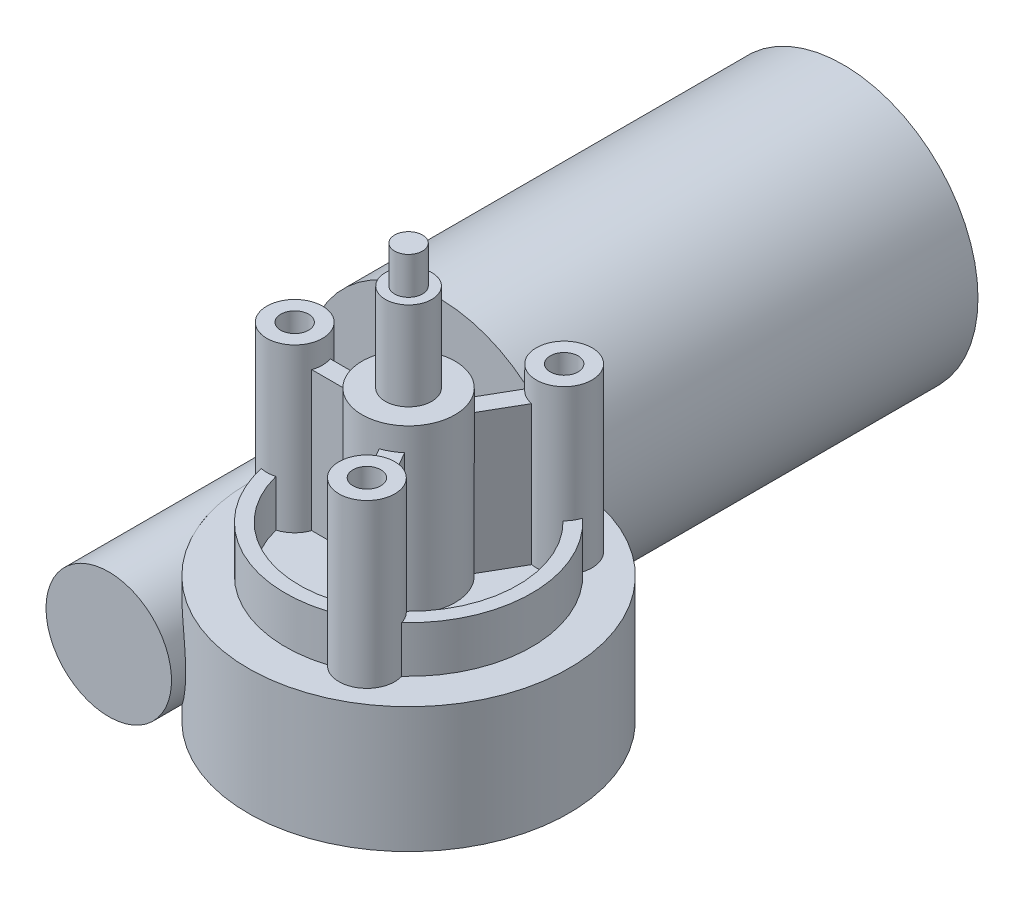
SolidWorks part; units mm, degrees
ref_plane "Front Plane" through (0, 0, 0) normal (0, 0, 1) x (1, 0, 0)
ref_plane "Top Plane" through (0, 0, 0) normal (0, 1, 0) x (1, 0, 0)
ref_plane "Right Plane" through (0, 0, 0) normal (1, 0, 0) x (0, 0, -1)
sketch "Sketch1" plane through (0, 0, 0) normal (0, 0, 1) x (1, 0, 0)
  circle A0 centre (0, 0) radius 29
  dimension "D1" = 58
extrude "Boss-Extrude1" add sketch "Sketch1" along normal blind 87
sketch "Sketch3" plane through (0, 0, 0) normal (0, 1, 0) x (1, 0, 0)
  line L0 (0, 0) -> (0, -87) construction
  line L1 (-29, -87) -> (29, -87) construction
  line L3 (0, 10) -> (-13.5, 10)
  line L4 (0, 10) -> (0, -158)
  line L5 (0, -158) -> (-13.5, -158)
  line L6 (-13.5, 10) -> (-13.5, -158)
  dimension "D3" = 13.5
  dimension "D1" = 168
  dimension "D2" = 10
revolve "Revolve1" add sketch "Sketch3" angle 360 about L0
sketch "Sketch4" plane through (0, 0, 0) normal (0, 1, 0) x (1, 0, 0)
  line L0 (0, -87) -> (0, 0) construction
  line L1 (-13.5, -87) -> (13.5, -87) construction
  line L2 (33, -161) -> (75.2332, -161) construction
  line L3 (13.5, 10) -> (-13.5, 10) construction
  circle A0 centre (33, -126.5) radius 34.5
  dimension "D1" = 69
  dimension "D2" = 33
  dimension "D3" = 171
extrude "Boss-Extrude2" add sketch "Sketch4" along normal mid plane 27
sketch "Sketch5" plane through (0, 13.5, 0) normal (0, 1, 0) x (1, 0, 0)
  line L0 (-1.5, -126.5) -> (67.5, -126.5) construction
  line L1 (33, -92) -> (33, -161) construction
  arc A0 (0, -116.4377) -> (0, -136.5623) centre (33, -126.5) ccw construction
  arc A1 (0, -136.5623) -> (0, -116.4377) centre (33, -126.5) ccw construction
  circle A2 centre (33, -126.5) radius 24.5 construction
  circle A3 centre (8.5, -126.5) radius 6
  circle A4 centre (33, -126.5) radius 10
  circle A5 centre (45.25, -105.2824) radius 6
  circle A6 centre (45.25, -147.7176) radius 6
  point P22 (33, -126.5)
  dimension "D1" = 49
  dimension "D2" = 20
  dimension "D3" = 12
  dimension "D4" = 3
extrude "Boss-Extrude3" add sketch "Sketch5" along normal blind 35
sketch "Sketch6" plane through (0, 13.5, 0) normal (0, 1, 0) x (1, 0, 0)
  line L0 (33, -126.5) -> (2.5, -126.5) construction
  line L1 (33, -161) -> (33, -92) construction
  line L2 (33, -126.5) -> (48.25, -100.0862) construction
  line L3 (33, -126.5) -> (48.25, -152.9138) construction
  line L4 (31.8453, -128.5) -> (2.8431, -128.5)
  line L5 (31.8453, -124.5) -> (2.8431, -124.5)
  line L6 (36.0122, -125.2828) -> (36.1163, -127.8976)
  line L7 (2.8431, -128.5) -> (2.8431, -124.5)
  line L9 (31.8453, -124.5) -> (46.3464, -99.3834)
  line L10 (46.3464, -99.3834) -> (49.8105, -101.3834)
  line L11 (36.0122, -125.2828) -> (49.8105, -101.3834)
  line L12 (31.8453, -128.5) -> (46.3464, -153.6166)
  line L14 (49.8105, -151.6166) -> (46.3464, -153.6166)
  line L15 (36.1163, -127.8976) -> (49.8105, -151.6166)
  line L16 (34.7321, -125.5) -> (35.3094, -126.5) [skipped]
  line L17 (34.7321, -127.5) -> (35.3094, -126.5) [skipped]
  arc A0 (0, -136.5623) -> (0, -116.4377) centre (33, -126.5) ccw construction
  circle A1 centre (8.5, -126.5) radius 6 construction
  circle A2 centre (45.25, -105.2824) radius 6 construction
  circle A3 centre (45.25, -147.7176) radius 6 construction
  point P30 (33, -126.5)
  dimension "D1" = 4
  dimension "D2" = 3
extrude "Boss-Extrude4" add sketch "Sketch6" along normal blind 30
sketch "Sketch7" plane through (0, 13.5, 0) normal (0, 1, 0) x (1, 0, 0)
  line L0 (33, -92) -> (33, -161) construction
  line L1 (-1.5, -126.5) -> (67.5, -126.5) construction
  arc A0 (0, -136.5623) -> (0, -116.4377) centre (33, -126.5) ccw construction
  arc A1 (0, -116.4377) -> (0, -136.5623) centre (33, -126.5) ccw construction
  circle A2 centre (33, -126.5) radius 26.5
  circle A3 centre (33, -126.5) radius 23.5
  dimension "D1" = 47
  dimension "D2" = 53
extrude "Boss-Extrude5" add sketch "Sketch7" along normal blind 10
sketch "Sketch8" plane through (0, 48.5, 0) normal (0, 1, 0) x (1, 0, 0)
  line L0 (33, -92) -> (33, -126.5) construction
  circle A0 centre (8.5, -126.5) radius 3
  arc A1 (0, -136.5623) -> (0, -116.4377) centre (33, -126.5) ccw construction
  circle A2 centre (45.25, -105.2824) radius 3
  circle A3 centre (45.25, -147.7176) radius 3
  point P16 (33, -126.5)
  dimension "D1" = 6
  dimension "D2" = 3
extrude "Cut-Extrude1" cut sketch "Sketch8" against normal blind 18
sketch "Sketch9" plane through (0, 48.5, 0) normal (0, 1, 0) x (1, 0, 0)
  circle A0 centre (33, -126.5) radius 5
  dimension "D1" = 10
extrude "Boss-Extrude6" add sketch "Sketch9" along normal blind 19
sketch "Sketch10" plane through (0, 67.5, 0) normal (0, 1, 0) x (1, 0, 0)
  circle A0 centre (33, -126.5) radius 3
  dimension "D1" = 6
extrude "Boss-Extrude7" add sketch "Sketch10" along normal blind 8
